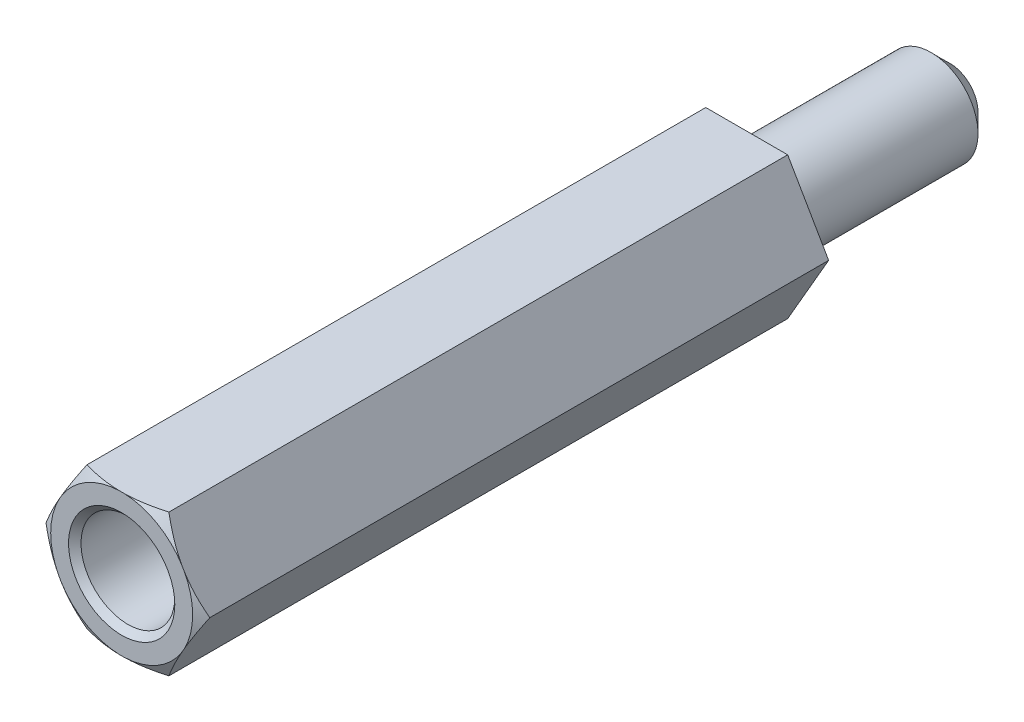
SolidWorks part; units mm, degrees
ref_plane "Front Plane" through (0, 0, 0) normal (0, 0, 1) x (1, 0, 0)
ref_plane "Top Plane" through (0, 0, 0) normal (0, 1, 0) x (1, 0, 0)
ref_plane "Right Plane" through (0, 0, 0) normal (1, 0, 0) x (0, 0, -1)
sketch "Sketch1" plane through (0, 0, 0) normal (0, 0, 1) x (1, 0, 0)
  line L0 (0, 0) -> (2.6212, 0) construction
  line L1 (2.6212, 0) -> (1.3106, 2.27)
  line L2 (1.3106, 2.27) -> (-1.3106, 2.27)
  line L3 (-1.3106, 2.27) -> (-2.6212, 0)
  line L4 (-2.6212, 0) -> (-1.3106, -2.27)
  line L5 (-1.3106, -2.27) -> (1.3106, -2.27)
  line L6 (1.3106, -2.27) -> (2.6212, 0)
  circle A0 centre (0, 0) radius 2.27 construction
  dimension "D1" = 4.54
extrude "Boss-Extrude1" add sketch "Sketch1" along normal blind 20
sketch "Sketch2" plane through (0, 0, 20) normal (0, 0, 1) x (1, 0, 0)
  circle A0 centre (0, 0) radius 1.5
extrude "Cut-Extrude1" cut sketch "Sketch2" against normal blind 12 and the other way through all
sketch "Sketch3" plane through (0, 0, 0) normal (0, 1, 0) x (1, 0, 0)
  line L0 (-2.6212, -20) -> (-2.2712, -20)
  line L1 (-2.2712, -20) -> (-2.6212, -19.8)
  line L2 (-2.6212, -20) -> (-2.6212, 0) construction
  line L3 (-2.6212, -19.8) -> (-2.6212, -20)
  dimension "D1" = 0.35
  dimension "D2" = 0.2
ref_axis "Axis1" through (0, 0, 8) along (0, 0, 1)
revolve "Cut-Revolve1" cut sketch "Sketch3" angle 360 about axis through (0, 0, 8) along (0, 0, 1)
ref_plane "Plane1" through (0, 0, 10) normal (0, 0, 1) x (1, 0, 0)
chamfer "Chamfer1" distance 0.2 angle 45 1 edges at (1.5, 0, 20)
sketch "Sketch4" plane through (0, 0, 0) normal (0, 0, -1) x (-1, 0, 0)
  circle A0 centre (0, 0) radius 1.5
extrude "Boss-Extrude2" add sketch "Sketch4" along normal blind 6.5
chamfer "Chamfer2" distance 0.6 angle 45 1 edges at (-1.5, 0, -6.5)
